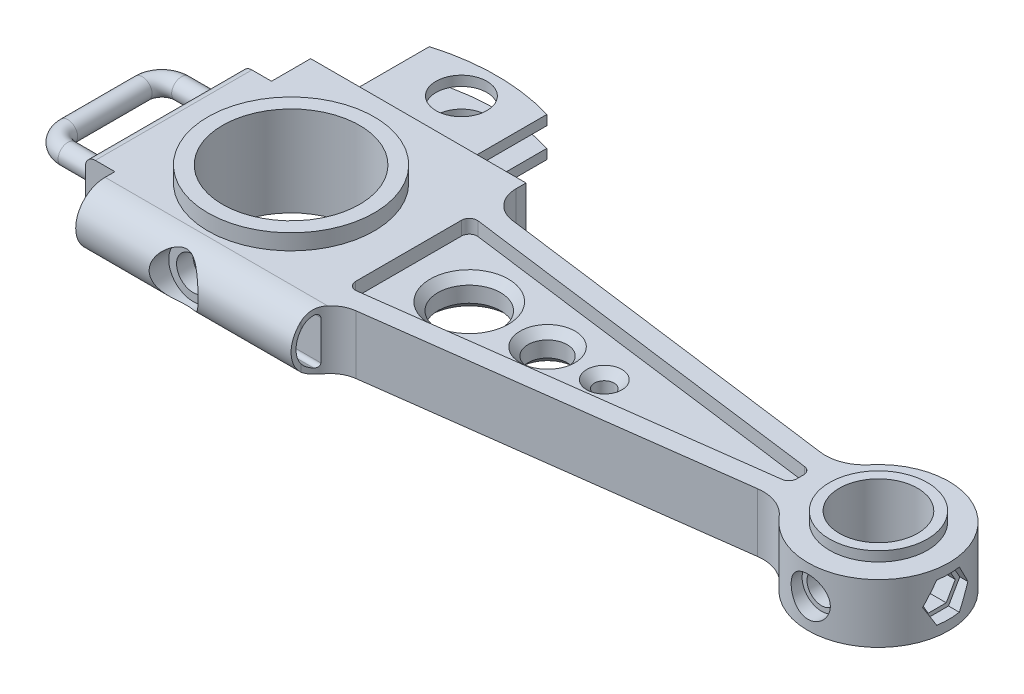
SolidWorks part; units mm, degrees
material "Cast Stainless Steel"
ref_plane "Front Plane" through (0, 0, 0) normal (0, 0, 1) x (1, 0, 0)
ref_plane "Top Plane" through (0, 0, 0) normal (0, 1, 0) x (1, 0, 0)
ref_plane "Right Plane" through (0, 0, 0) normal (1, 0, 0) x (0, 0, -1)
sketch "Sketch1" plane through (0, 0, 0) normal (0, 1, 0) x (1, 0, 0)
  line L0 (-41.275, 25.4) -> (-41.275, -25.4)
  line L1 (-41.275, -25.4) -> (-31.75, -25.4)
  line L2 (-31.75, -25.4) -> (-31.75, -38.1)
  line L3 (-31.75, -38.1) -> (38.1, -38.1)
  line L8 (38.1, -38.1) -> (38.1, -34.82)
  line L9 (38.1, 38.1) -> (-31.75, 38.1)
  line L10 (-31.75, 38.1) -> (-31.75, 25.4)
  line L11 (-31.75, 25.4) -> (-41.275, 25.4)
  line L12 (46.3817, 25.3765) -> (161.5575, 10.2133)
  line L13 (46.3817, -25.3765) -> (161.5575, -10.2133)
  line L14 (0, 0) -> (190.5, 0) construction
  line L15 (190.5, 0) -> (38.1, 20.0638) construction
  line L16 (190.5, 0) -> (38.1, -20.0638) construction
  line L17 (38.1, 34.82) -> (38.1, 38.1)
  circle A0 centre (0, 0) radius 22.225
  circle A1 centre (190.5, 0) radius 12.7
  arc A3 (172.9598, -14.6601) -> (172.9598, 14.6601) centre (190.5, 0) ccw
  arc A4 (46.3817, -25.3765) -> (38.1, -34.82) centre (47.625, -34.82) ccw
  arc A5 (46.3817, 25.3765) -> (38.1, 34.82) centre (47.625, 34.82) cw
  arc A6 (161.5575, 10.2133) -> (172.9598, 14.6601) centre (163.2152, 22.8047) ccw
  arc A7 (161.5575, -10.2133) -> (172.9598, -14.6601) centre (163.2152, -22.8047) cw
  point P25 (38.1, -26.4668)
  point P28 (38.1, 26.4668)
  dimension "D1" = 38.1
  dimension "D8" = 44.45
  dimension "D9" = 190.5
  dimension "D10" = 22.86
  dimension "D11" = 25.4
  dimension "D16" = 9.525
  dimension "D17" = 12.7
  dimension "D2" = 76.2
  dimension "D3" = 31.75
  dimension "D4" = 41.275
  dimension "D5" = 38.1
  dimension "D6" = 50.8
  dimension "D7" = 12.7
  dimension "D12" = 11.6332
  dimension "D13" = 15
  dimension "D14" = 11.6332
  dimension "D15" = 7.5
extrude "Boss-Extrude2" add sketch "Sketch1" along normal mid plane 19.05
sketch "Sketch3" plane through (0, 0, 0) normal (0, 1, 0) x (1, 0, 0)
  circle A0 centre (190.5, 0) radius 15.875
  circle A1 centre (190.5, 0) radius 12.7 construction
  circle A2 centre (190.5, 0) radius 12.7
  dimension "D1" = 31.75
extrude "Boss-Extrude3" add sketch "Sketch3" along normal mid plane 25.4
sketch "Sketch7" plane through (0, 0, 38.1) normal (0, 0, 1) x (1, 0, 0)
  circle A0 centre (0, 0) radius 5.3975
  dimension "D1" = 10.795
extrude "Cut-Extrude5" cut sketch "Sketch7" against normal up to next
sketch "Sketch8" plane through (0, 0, 38.1) normal (0, 0, 1) x (1, 0, 0)
  circle A0 centre (0, 0) radius 7.9375
  dimension "D1" = 15.875
extrude "Cut-Extrude6" cut sketch "Sketch8" against normal blind 6.35
sketch "Sketch4" plane through (0, 0, 0) normal (0, 1, 0) x (1, 0, 0)
  circle A0 centre (0, 0) radius 26.9875
  circle A1 centre (0, 0) radius 22.225 construction
  circle A2 centre (0, 0) radius 22.225
  dimension "D1" = 53.975
extrude "Boss-Extrude4" add sketch "Sketch4" along normal mid plane 29.21
sketch "Sketch5" plane through (0, 0, 0) normal (1, 0, 0) x (0, 0, -1)
  line L0 (-28.575, 9.525) -> (0, 9.525) construction
  line L1 (22.86, 9.525) -> (-22.86, 9.525) construction
  line L2 (0, 9.525) -> (0, -9.525) construction
  line L3 (-22.86, -9.525) -> (22.86, -9.525) construction
  line L4 (0, -9.525) -> (-28.575, -9.525) construction
  line L6 (-38.1, 9.525) -> (-38.1, -9.525)
  line L9 (-28.575, -9.525) -> (-38.1, -9.525)
  line L10 (-38.1, 9.525) -> (-38.1, -9.525) construction
  line L11 (-38.1, 9.525) -> (-28.575, 9.525)
  arc A0 (-28.575, 9.525) -> (-28.575, -9.525) centre (-28.575, 0) ccw
  point P2 (-28.575, 0)
  dimension "D1" = 28.575
  dimension "D2" = 9.525
extrude "Cut-Extrude2" cut sketch "Sketch5" against normal mid plane 81.28 contours A0 L11 L6 | A0 L6 L9
sketch "Sketch6" plane through (38.1, 0, 0) normal (1, 0, 0) x (0, 0, -1)
  line L0 (-29.845, 6.338) -> (-29.845, -6.338)
  line L1 (22.86, -9.525) -> (22.86, 9.525) construction
  arc A0 (-31.3947, 7.4062) -> (-31.3947, -7.4062) centre (-28.575, 0) ccw
  arc A1 (-29.845, -6.338) -> (-31.3947, -7.4062) centre (-30.988, -6.338) cw
  arc A2 (-29.845, 6.338) -> (-31.3947, 7.4062) centre (-30.988, 6.338) ccw
  dimension "D1" = 15.8496
  dimension "D3" = 1.143
  dimension "D2" = 1.27
extrude "Cut-Extrude4" cut sketch "Sketch6" against normal mid plane 25.4
sketch "Sketch10" plane through (0, 0, 0) normal (0, 1, 0) x (1, 0, 0)
  line L0 (-19.05, 38.1) -> (-19.05, 63.8956)
  line L1 (38.1, 38.1) -> (-31.75, 38.1) construction
  line L3 (19.05, 63.8956) -> (19.05, 38.1)
  line L4 (-19.05, 38.1) -> (19.05, 38.1)
  arc A0 (19.05, 63.8956) -> (-19.05, 63.8956) centre (0, 0) ccw
  circle A1 centre (0, 55.245) radius 8.255
  dimension "D2" = 133.35
  dimension "D4" = 16.51
  dimension "D1" = 38.1
  dimension "D3" = 19.05
  dimension "D5" = 17.145
extrude "Boss-Extrude5" add sketch "Sketch10" along normal mid plane 12.7
fillet "Fillet1" radius 1.27 4 edges at (19.05, 0, -38.1) (0, -6.35, -38.1) (-19.05, 0, -38.1) (0, 6.35, -38.1)
sketch "Sketch11" plane through (19.05, 0, 0) normal (1, 0, 0) x (0, 0, -1)
  line L0 (41.91, 3.175) -> (41.91, -3.175)
  line L1 (41.91, -3.175) -> (66.675, -3.175)
  line L2 (66.675, -3.175) -> (66.675, 3.175)
  line L3 (66.675, 3.175) -> (41.91, 3.175)
  line L4 (38.1, 9.525) -> (38.1, -9.525) construction
  point P2 (66.675, 0)
  dimension "D1" = 6.35
  dimension "D2" = 3.81
extrude "Cut-Extrude7" cut sketch "Sketch11" against normal through all
sketch "Sketch12" plane through (-41.275, 0, 0) normal (-1, 0, 0) x (0, 0, 1)
  circle A0 centre (18.415, 0) radius 3.175
  dimension "D1" = 6.35
  dimension "D2" = 18.415
sketch "Sketch13" plane through (0, 0, 0) normal (0, 1, 0) x (1, 0, 0)
  line L0 (-41.275, -18.415) -> (-53.975, -18.415)
  line L1 (-41.275, -15.24) -> (-41.275, -21.59) construction
  line L2 (-60.325, -12.065) -> (-60.325, 12.065)
  line L3 (-53.975, 18.415) -> (-41.275, 18.415)
  line L4 (-41.275, 25.4) -> (-41.275, -25.4) construction
  arc A0 (-53.975, -18.415) -> (-60.325, -12.065) centre (-53.975, -12.065) cw
  arc A1 (-60.325, 12.065) -> (-53.975, 18.415) centre (-53.975, 12.065) cw
  dimension "D3" = 6.35
  dimension "D1" = 36.83
  dimension "D2" = 19.05
sweep "Sweep1" add profiles "Sketch12" path "Sketch13"
fillet "Fillet2" radius 2.54 2 edges at (-41.275, 0, 21.59) (-41.275, 0, -21.59)
fillet "Fillet3" radius 3.175 2 edges at (-41.275, -9.525, 0) (-41.275, 9.525, 0)
sketch "Sketch14" plane through (0, 9.525, 0) normal (0, 1, 0) x (1, 0, 0)
  line L0 (38.1, 17.1675) -> (38.1, -17.1675)
  line L1 (40.9715, -19.6858) -> (162.8915, -3.6347)
  line L2 (162.8915, 3.6347) -> (40.9715, 19.6858)
  line L3 (0, 0) -> (190.5, 0) construction
  line L5 (165.1, -1.1165) -> (165.1, 1.1165)
  arc A0 (165.1, -1.1165) -> (162.8915, -3.6347) centre (162.56, -1.1165) cw
  arc A1 (165.1, 1.1165) -> (162.8915, 3.6347) centre (162.56, 1.1165) ccw
  arc A2 (38.1, -17.1675) -> (40.9715, -19.6858) centre (40.64, -17.1675) ccw
  arc A3 (38.1, 17.1675) -> (40.9715, 19.6858) centre (40.64, 17.1675) cw
  dimension "D4" = 2.54
  dimension "D1" = 7.5
  dimension "D2" = 15
  dimension "D3" = 25.4
extrude "Cut-Extrude8" cut sketch "Sketch14" against normal blind 4.445
mirror "Mirror1" about plane through (0, 0, 0) normal (0, 1, 0) of "Cut-Extrude8"
sketch "Sketch15" plane through (0, 5.08, 0) normal (0, 1, 0) x (1, 0, 0)
  circle A0 centre (57.785, 0) radius 10.16
  circle A1 centre (83.185, 0) radius 6.35
  circle A2 centre (101.6, 0) radius 3.175
  circle A3 centre (190.5, 0) radius 15.875 construction
  dimension "D1" = 25.4
  dimension "D4" = 20.32
  dimension "D5" = 12.7
  dimension "D6" = 6.35
  dimension "D2" = 18.415
  dimension "D3" = 88.9
extrude "Cut-Extrude9" cut sketch "Sketch15" against normal through all
chamfer "Chamfer1" distance 2.54 angle 45 6 edges at (101.6, -5.08, 3.175) (101.6, 5.08, 3.175) (83.185, -5.08, 6.35) (83.185, 5.08, 6.35) (57.785, -5.08, 10.16) (57.785, 5.08, 10.16)
sketch "Sketch16" plane through (0, 0, 0) normal (0, 0, 1) x (1, 0, 0)
  circle A0 centre (190.5, 0) radius 4.7625
  dimension "D1" = 9.525
  dimension "D2" = 190.5
extrude "Cut-Extrude10" cut sketch "Sketch16" along normal through all
sketch "Sketch17" plane through (0, 0, 0) normal (0, 0, 1) x (1, 0, 0)
  circle A0 centre (190.5, 0) radius 6.35
  dimension "D1" = 12.7
extrude "Cut-Extrude11" cut sketch "Sketch17" along normal blind 4.445 from offset 18.415
sketch "Sketch18" plane through (0, 0, 0) normal (1, 0, 0) x (0, 0, -1)
  line L1 (5.8659, 0) -> (2.9329, 5.08)
  line L2 (2.9329, 5.08) -> (-2.9329, 5.08)
  line L3 (-2.9329, 5.08) -> (-5.8659, 0)
  line L4 (-5.8659, 0) -> (-2.9329, -5.08)
  line L5 (-2.9329, -5.08) -> (2.9329, -5.08)
  line L6 (2.9329, -5.08) -> (5.8659, 0)
  circle A0 centre (0, 0) radius 5.08 construction
  dimension "D1" = 10.16
extrude "Cut-Extrude12" cut sketch "Sketch18" along normal through all from offset 190.5
sketch "Sketch19" plane through (0, 0, 0) normal (1, 0, 0) x (0, 0, -1)
  line L1 (7.3323, 0) -> (3.6662, 6.35)
  line L2 (3.6662, 6.35) -> (-3.6662, 6.35)
  line L3 (-3.6662, 6.35) -> (-7.3323, 0)
  line L4 (-7.3323, 0) -> (-3.6662, -6.35)
  line L5 (-3.6662, -6.35) -> (3.6662, -6.35)
  line L6 (3.6662, -6.35) -> (7.3323, 0)
  circle A0 centre (0, 0) radius 6.35 construction
  dimension "D1" = 12.7
extrude "Cut-Extrude13" cut sketch "Sketch19" along normal through all from offset 209.55
sketch "Sketch20"
  dimension "D1" = 9.525
